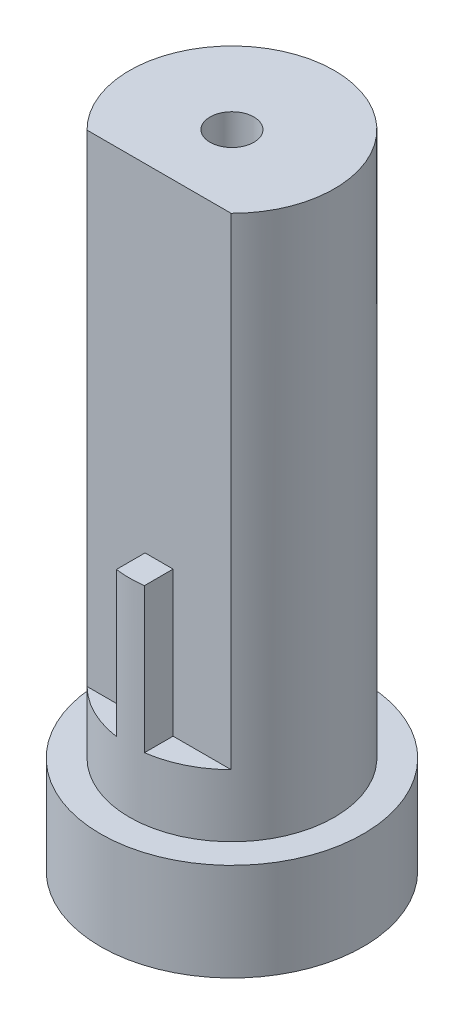
SolidWorks part; units mm, degrees
ref_plane "Front Plane" through (0, 0, 0) normal (0, 0, 1) x (1, 0, 0)
ref_plane "Top Plane" through (0, 0, 0) normal (0, 1, 0) x (1, 0, 0)
ref_plane "Right Plane" through (0, 0, 0) normal (1, 0, 0) x (0, 0, -1)
sketch "Sketch1" plane through (0, 0, 0) normal (0, 1, 0) x (1, 0, 0)
  circle A0 centre (0, 0) radius 9.005
  dimension "D1" = 18.01
extrude "Base Ring" add sketch "Sketch1" along normal blind 6.69
sketch "Sketch2" plane through (0, 0, 0) normal (0, 1, 0) x (1, 0, 0)
  circle A0 centre (0, 0) radius 7.025
  dimension "D1" = 14.05
extrude "Main Cylinder" add sketch "Sketch2" along normal blind 44
ref_plane "Top Main Cyl. Ref." through (0, 44, 0) normal (0, 1, 0) x (1, 0, 0)
sketch "Sketch3" plane through (0, 44, 0) normal (0, 1, 0) x (1, 0, 0)
  line L0 (-4.9397, -4.995) -> (-0.96, -4.995)
  line L1 (0, 7.025) -> (11.4415, 7.025) construction
  line L2 (0, -9.9055) -> (0, 9.9055) construction
  line L3 (-0.96, -4.995) -> (-0.96, -6.9591)
  line L4 (0.96, -4.995) -> (0.96, -6.9591)
  line L5 (0.96, -4.995) -> (4.9397, -4.995)
  circle A0 centre (0, 0) radius 7.025 construction
  circle A1 centre (0, 0) radius 7.025 construction
  arc A2 (-4.9397, -4.995) -> (-0.96, -6.9591) centre (0, 0) ccw
  arc A3 (0.96, -6.9591) -> (4.9397, -4.995) centre (0, 0) ccw
  dimension "D1" = 12.02
  dimension "D2" = 0.96
  dimension "D3" = 0.96
extrude "Cutout pt1" cut sketch "Sketch3" against normal blind 33.03
sketch "Sketch4" plane through (0, 44, 0) normal (0, 1, 0) x (1, 0, 0)
  line L0 (-0.96, -4.995) -> (0.96, -4.995)
  line L1 (0.96, -4.995) -> (0.96, -6.9591)
  line L2 (-0.96, -4.995) -> (-0.96, -6.9591)
  arc A0 (-0.96, -6.9591) -> (0.96, -6.9591) centre (0, 0) ccw
extrude "Cutout pt2" cut sketch "Sketch4" against normal blind 23.11
sketch "Sketch5" plane through (0, 44, 0) normal (0, 1, 0) x (1, 0, 0)
  circle A0 centre (0, 0) radius 1.505
  dimension "D1" = 3.01
extrude "Top Hole" cut sketch "Sketch5" against normal through all
sketch "Sketch7" plane through (0, 0, 0) normal (0, 1, 0) x (1, 0, 0)
  circle A0 centre (0, 0) radius 7.875
  dimension "D1" = 15.75
extrude "Cut-Extrude4" cut sketch "Sketch7" along normal blind 5.42
sketch "Sketch8" plane through (0, 0, 0) normal (0, 1, 0) x (1, 0, 0)
  circle A0 centre (0, 0) radius 5.76
  dimension "D1" = 11.52
extrude "Cut-Extrude5" cut sketch "Sketch8" along normal blind 8.86
sketch "Sketch9" plane through (0, 0, 0) normal (0, 1, 0) x (1, 0, 0)
  line L0 (4.3375, -3.79) -> (-4.3375, -3.79)
  line L1 (0, 5.76) -> (7.4996, 5.76) construction
  arc A0 (4.3375, -3.79) -> (-4.3375, -3.79) centre (0, 0) ccw
  dimension "D1" = 11.52
  dimension "D2" = 9.55
extrude "Cut-Extrude6" cut sketch "Sketch9" along normal blind 40.88
sketch "Sketch10" plane through (0, 0, 0) normal (0, 1, 0) x (1, 0, 0)
  line L0 (16.0783, 0) -> (-15.9195, 0) construction
  line L1 (-7.875, 17.4474) -> (-7.875, -13.1873) construction
  circle A1 centre (0, 0) radius 7.875 construction
ref_plane "Plane2" through (-7.875, 0, 0) normal (-1, 0, 0) x (0, 0, 1)
sketch "Sketch11" plane through (-7.875, 0, 0) normal (-1, 0, 0) x (0, 0, 1)
  line L0 (0, 0.4817) -> (-4.005, 2.5817)
  line L1 (0, -17.5988) -> (0, 17.5988) construction
  line L2 (0, 0.4817) -> (4.005, 2.5817)
  line L3 (-4.005, 2.5817) -> (-4.005, 6.69)
  line L4 (4.005, 2.5817) -> (4.005, 6.69)
  line L5 (-4.005, 6.69) -> (4.005, 6.69)
  line L6 (9.005, 6.69) -> (-9.005, 6.69) construction
  line L7 (-7.875, 5.42) -> (7.875, 5.42) construction
  dimension "D1" = 8.01
  dimension "D2" = 2.1
  dimension "D3" = 4.9383
sketch "Sketch12" plane through (0, 0, 0) normal (1, 0, 0) x (0, 0, -1)
  point P0 (0, 0)
ref_plane "Plane3" through (0, 5.42, 0) normal (0, -1, 0) x (-1, 0, 0)
sketch "Sketch13" plane through (0, 5.42, 0) normal (0, -1, 0) x (-1, 0, 0)
  point P0 (0, 0)
